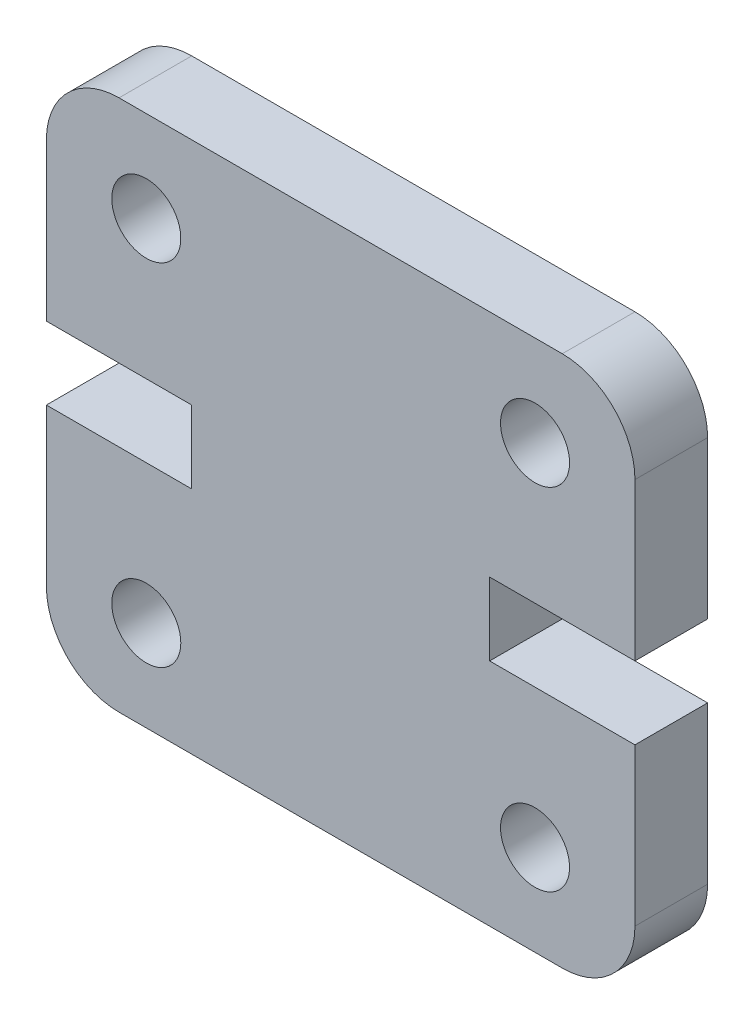
SolidWorks part; units mm, degrees
ref_plane "Front Plane" through (0, 0, 0) normal (0, 0, 1) x (1, 0, 0)
ref_plane "Top Plane" through (0, 0, 0) normal (0, 1, 0) x (1, 0, 0)
ref_plane "Right Plane" through (0, 0, 0) normal (1, 0, 0) x (0, 0, -1)
sketch "Sketch1" plane through (0, 0, 0) normal (0, 0, 1) x (1, 0, 0)
  line L0 (8.1, 14.645) -> (8.1, 0) construction
  line L1 (0, 7.3225) -> (16.2, 7.3225) construction
  line L2 (2, 14.645) -> (14.2, 14.645)
  line L3 (0, 8.3225) -> (4, 8.3225)
  line L4 (0, 8.3225) -> (0, 12.645)
  line L5 (12.2, 6.3225) -> (12.2, 8.3225)
  line L6 (16.2, 6.3225) -> (12.2, 6.3225)
  line L7 (16.2, 6.3225) -> (16.2, 2)
  line L8 (16.2, 8.3225) -> (16.2, 12.645)
  line L9 (16.2, 8.3225) -> (12.2, 8.3225)
  line L12 (0, 6.3225) -> (0, 2)
  line L17 (0, 6.3225) -> (4, 6.3225)
  line L18 (4, 6.3225) -> (4, 8.3225)
  line L19 (2, 0) -> (14.2, 0)
  circle A0 centre (2.75, 12.145) radius 0.95
  arc A1 (0, 12.645) -> (2, 14.645) centre (2, 12.645) cw
  circle A2 centre (13.45, 2.5) radius 0.95
  arc A3 (16.2, 2) -> (14.2, 0) centre (14.2, 2) cw
  arc A4 (16.2, 12.645) -> (14.2, 14.645) centre (14.2, 12.645) ccw
  circle A5 centre (13.45, 12.145) radius 0.95
  arc A11 (0, 2) -> (2, 0) centre (2, 2) ccw
  circle A13 centre (2.75, 2.5) radius 0.95
  point P9 (4, 7.3225)
  point P14 (8.1, 7.3225)
  point P27 (12.2, 7.3225)
  dimension "D1" = 1
  dimension "D2" = 2
  dimension "D8" = 1.9
  dimension "D3" = 2.75
  dimension "D4" = 8.1
  dimension "D5" = 2.5
  dimension "D6" = 6.3225
  dimension "D7" = 4
extrude "Boss-Extrude1" add sketch "Sketch1" along normal blind 4
sketch "Sketch2" plane through (0, 0, 0) normal (0, 0, -1) x (-1, 0, 0)
  line L0 (0, 0) -> (-16.2, 0)
  line L1 (-16.2, 0) -> (-16.2, 14.645)
  line L2 (-16.2, 14.645) -> (0, 14.645)
  line L3 (0, 14.645) -> (0, 0)
extrude "Cut-Extrude1" cut sketch "Sketch2" against normal blind 2
equation "\"D4@Sketch1\"= \"fingerWidth@parametersSketch@prostheticParameters.SLDPRT\" / 2'MIP width"
equation "\"D6@Sketch1\"=( \"HL@parametersSketch@prostheticParameters.SLDPRT\" * 0.117 - 4 - 3 - 2) / 2 'MIP length - Sil. Sht DIP - Sil. Sht MIP"
equation "\"D8@Sketch1\"= 1.5 + \"tol1@parametersSketch@prostheticParameters.SLDPRT\""
